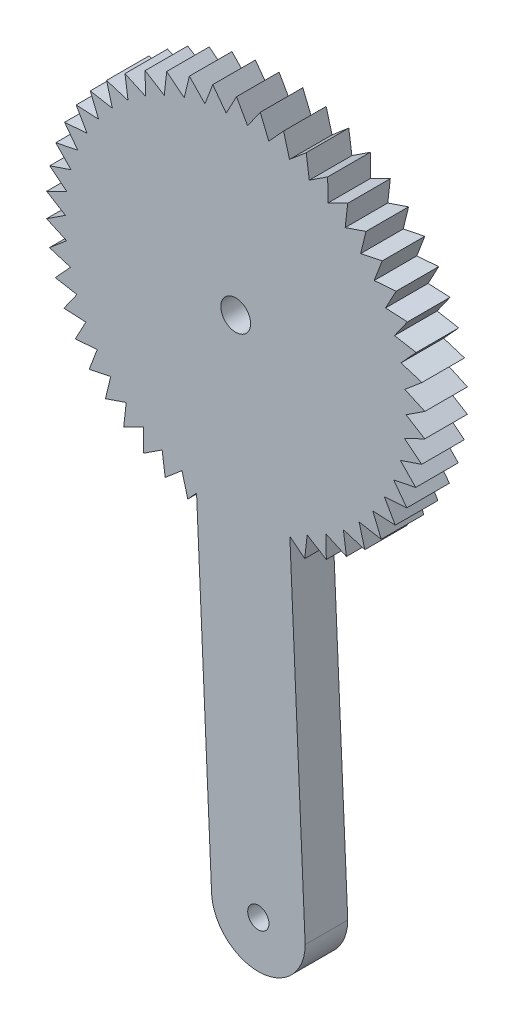
SolidWorks part; units mm, degrees
ref_plane "Front Plane" through (0, 0, 0) normal (0, 0, 1) x (1, 0, 0)
ref_plane "Top Plane" through (0, 0, 0) normal (0, 1, 0) x (1, 0, 0)
ref_plane "Right Plane" through (0, 0, 0) normal (1, 0, 0) x (0, 0, -1)
sketch "Sketch1" plane through (0, 0, 0) normal (0, 0, 1) x (1, 0, 0)
  line L0 (348.0465, 372.4188) -> (349.2577, 374.6999)
  line L1 (348.0465, 372.4188) -> (346.4683, 374.5361)
  line L2 (350.5581, 372.4015) -> (349.2577, 374.6999)
  line L3 (350.5581, 372.4015) -> (352.0456, 374.5128)
  line L4 (353.0477, 372.0695) -> (352.0456, 374.5128)
  line L5 (353.0477, 372.0695) -> (354.7881, 373.9777)
  line L6 (355.476, 371.4281) -> (354.7881, 373.9777)
  line L7 (355.476, 371.4281) -> (357.4418, 373.1032)
  line L8 (357.8048, 370.4875) -> (357.4418, 373.1032)
  line L9 (357.8048, 370.4875) -> (359.9651, 371.9029)
  line L10 (359.9974, 369.2623) -> (359.9651, 371.9029)
  line L11 (359.9974, 369.2623) -> (362.318, 370.3958)
  line L12 (362.0191, 367.772) -> (362.318, 370.3958)
  line L13 (362.0191, 367.772) -> (364.4635, 368.6058)
  line L14 (363.8381, 366.0401) -> (364.4635, 368.6058)
  line L15 (363.8381, 366.0401) -> (366.3677, 366.5609)
  line L16 (365.4256, 364.0939) -> (366.3677, 366.5609)
  line L17 (365.4256, 364.0939) -> (368.0006, 364.2935)
  line L18 (366.7568, 361.964) -> (368.0006, 364.2935)
  line L19 (366.7568, 361.964) -> (369.3364, 361.8393)
  line L20 (367.8105, 359.6841) -> (369.3364, 361.8393)
  line L21 (367.8105, 359.6841) -> (370.3542, 359.2371)
  line L22 (368.5701, 357.2901) -> (370.3542, 359.2371)
  line L23 (368.5701, 357.2901) -> (371.0377, 356.5278)
  line L24 (369.0237, 354.8198) -> (371.0377, 356.5278)
  line L25 (369.0237, 354.8198) -> (371.3763, 353.7542)
  line L26 (369.1641, 352.3121) -> (371.3763, 353.7542)
  line L27 (369.1641, 352.3121) -> (371.3646, 350.9601)
  line L28 (368.9891, 349.8066) -> (371.3646, 350.9601)
  line L29 (368.9891, 349.8066) -> (371.0028, 348.1894)
  line L30 (368.5014, 347.3427) -> (371.0028, 348.1894)
  line L31 (368.5014, 347.3427) -> (370.2966, 345.486)
  line L32 (367.7088, 344.9595) -> (370.2966, 345.486)
  line L33 (367.7088, 344.9595) -> (369.2571, 342.8923)
  line L34 (366.6238, 342.6943) -> (369.2571, 342.8923)
  line L35 (366.6238, 342.6943) -> (367.9008, 340.4494)
  line L36 (365.2634, 340.583) -> (367.9008, 340.4494)
  line L37 (365.2634, 340.583) -> (366.249, 338.1958)
  line L38 (363.6491, 338.6589) -> (366.249, 338.1958)
  line L39 (363.6491, 338.6589) -> (364.3277, 336.1669)
  line L40 (361.8064, 336.9522) -> (364.3277, 336.1669)
  line L41 (361.8064, 336.9522) -> (362.1673, 334.3949)
  line L42 (359.7643, 335.49) -> (362.1673, 334.3949)
  line L43 (359.7643, 335.49) -> (359.8019, 332.9076)
  line L44 (357.5551, 334.2952) -> (359.8019, 332.9076)
  line L45 (357.5551, 334.2952) -> (357.2687, 331.7285)
  line L46 (355.5205, 333.1391) -> (357.2687, 331.7285)
  line L47 (344.5688, 332.0493) -> (343.5411, 330.9225)
  line L48 (342.8531, 333.4721) -> (343.5411, 330.9225)
  line L49 (342.8531, 333.4721) -> (340.8873, 331.797)
  line L50 (340.5243, 334.4128) -> (340.8873, 331.797)
  line L51 (340.5243, 334.4128) -> (338.364, 332.9973)
  line L52 (338.3317, 335.6379) -> (338.364, 332.9973)
  line L53 (338.3317, 335.6379) -> (336.0111, 334.5044)
  line L54 (336.31, 337.1282) -> (336.0111, 334.5044)
  line L55 (336.31, 337.1282) -> (333.8656, 336.2944)
  line L56 (334.491, 338.8601) -> (333.8656, 336.2944)
  line L57 (334.491, 338.8601) -> (331.9614, 338.3393)
  line L58 (332.9035, 340.8063) -> (331.9614, 338.3393)
  line L59 (332.9035, 340.8063) -> (330.3285, 340.6067)
  line L60 (331.5723, 342.9362) -> (330.3285, 340.6067)
  line L61 (331.5723, 342.9362) -> (328.9927, 343.0609)
  line L62 (330.5187, 345.2161) -> (328.9927, 343.0609)
  line L63 (330.5187, 345.2161) -> (327.975, 345.6631)
  line L64 (329.759, 347.6101) -> (327.975, 345.6631)
  line L65 (329.759, 347.6101) -> (327.2914, 348.3724)
  line L66 (329.3054, 350.0804) -> (327.2914, 348.3724)
  line L67 (329.3054, 350.0804) -> (326.9528, 351.146)
  line L68 (329.165, 352.5881) -> (326.9528, 351.146)
  line L69 (329.165, 352.5881) -> (326.9645, 353.9401)
  line L70 (329.34, 355.0936) -> (326.9645, 353.9401)
  line L71 (329.34, 355.0936) -> (327.3263, 356.7108)
  line L72 (329.8277, 357.5575) -> (327.3263, 356.7108)
  line L73 (329.8277, 357.5575) -> (328.0325, 359.4142)
  line L74 (330.6203, 359.9407) -> (328.0325, 359.4142)
  line L75 (330.6203, 359.9407) -> (329.072, 362.0079)
  line L76 (331.7053, 362.2059) -> (329.072, 362.0079)
  line L77 (331.7053, 362.2059) -> (330.4283, 364.4508)
  line L78 (333.0657, 364.3172) -> (330.4283, 364.4508)
  line L79 (333.0657, 364.3172) -> (332.0801, 366.7044)
  line L80 (334.68, 366.2413) -> (332.0801, 366.7044)
  line L81 (334.68, 366.2413) -> (334.0014, 368.7333)
  line L82 (336.5227, 367.948) -> (334.0014, 368.7333)
  line L83 (336.5227, 367.948) -> (336.1618, 370.5053)
  line L84 (338.5648, 369.4102) -> (336.1618, 370.5053)
  line L85 (338.5648, 369.4102) -> (338.5272, 371.9926)
  line L86 (340.7741, 370.605) -> (338.5272, 371.9926)
  line L87 (340.7741, 370.605) -> (341.0604, 373.1717)
  line L88 (343.1156, 371.5134) -> (341.0604, 373.1717)
  line L89 (343.1156, 371.5134) -> (343.7215, 374.0241)
  line L90 (345.5526, 372.1212) -> (343.7215, 374.0241)
  line L91 (345.5526, 372.1212) -> (346.4683, 374.5361)
  line L93 (344.5688, 332.0493) -> (346.3214, 292.509)
  line L95 (357.3214, 292.509) -> (355.5205, 333.1391)
  arc A0 (346.3214, 292.509) -> (357.2998, 292.9956) centre (351.8214, 292.509) ccw
  circle A7 centre (349.1646, 352.4501) radius 1.75
  circle A8 centre (351.8214, 292.509) radius 1.25
  point P144 (349.1646, 352.4501)
  dimension "D1" = 60
  dimension "D4" = 3.5
extrude "Boss-Extrude2" add sketch "Sketch1" along normal blind 5 contours L93 A0 L95 L46 L45 L44 L43 L42 L41 L40 L39 L38 L37 L36 L35 L34 L33 L32 L31 L30 L29 L28 L27 L26 L25 L24 L23 L22 L21 L20 L19 L18 L17 L16 L15 L14 L13 L12 L11 L10 L9 L8 L7 L6 L5 L4 L3 L2 L0 L1
